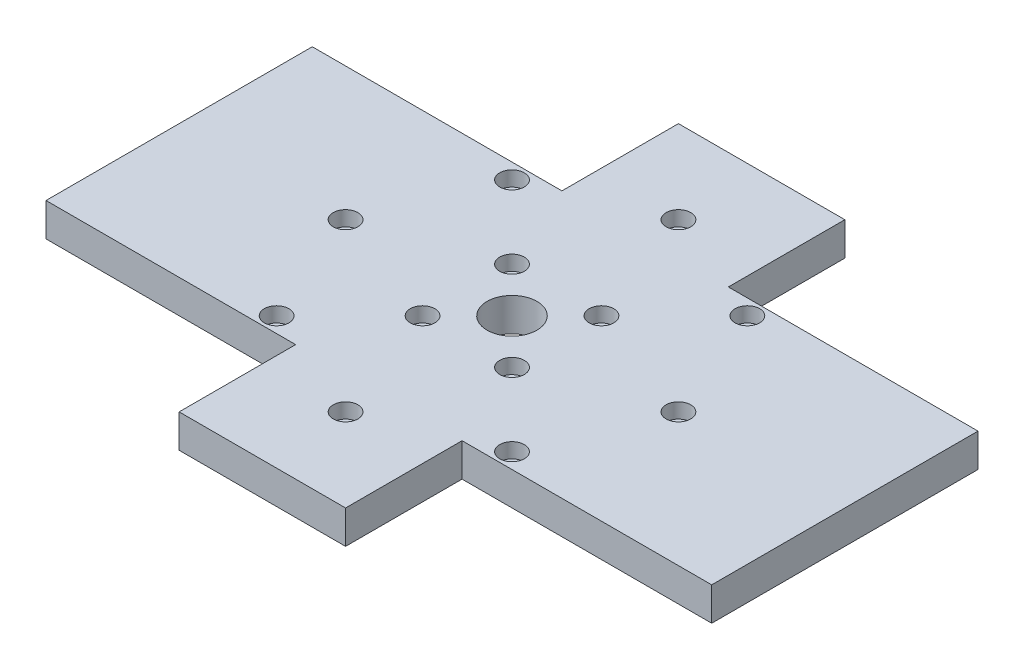
SolidWorks part; units mm, degrees
ref_plane "前视基准面" through (0, 0, 0) normal (0, 0, 1) x (1, 0, 0)
ref_plane "上视基准面" through (0, 0, 0) normal (0, 1, 0) x (1, 0, 0)
ref_plane "右视基准面" through (0, 0, 0) normal (1, 0, 0) x (0, 0, -1)
sketch "草图1" plane through (0, 0, 0) normal (0, 1, 0) x (1, 0, 0)
  line L1 (-100, 40) -> (100, 40)
  line L2 (-100, 40) -> (-100, -40)
  line L3 (-100, -40) -> (100, -40)
  line L4 (100, 40) -> (100, -40)
  line L5 (-100, 40) -> (100, -40) construction
  line L6 (-100, -40) -> (100, 40) construction
  point P0 (0, 0)
  dimension "D1" = 80
  dimension "D2" = 200
extrude "凸台-拉伸1" add sketch "草图1" along normal blind 10
sketch "草图3" plane through (0, 10, 0) normal (0, 1, 0) x (1, 0, 0)
  line L1 (-25, -75) -> (25, -75)
  line L2 (-25, -75) -> (-25, 75)
  line L3 (-25, 75) -> (25, 75)
  line L4 (25, -75) -> (25, 75)
  line L5 (-25, -75) -> (25, 75) construction
  line L6 (-25, 75) -> (25, -75) construction
  point P0 (0, 0)
  dimension "D1" = 150
  dimension "D2" = 50
extrude "凸台-拉伸2" add sketch "草图3" against normal blind 10
sketch "草图5" plane through (0, 10, 0) normal (0, 1, 0) x (1, 0, 0)
  line L0 (0, 0) -> (46.2802, 0) construction
  line L1 (0, 0) -> (16.9009, 16.9009) construction
  circle A0 centre (0, 0) radius 19 construction
  circle A1 centre (13.435, 13.435) radius 1.7
  circle A2 centre (13.435, -13.435) radius 1.7
  circle A3 centre (-13.435, -13.435) radius 1.7
  circle A4 centre (-13.435, 13.435) radius 1.7
  circle A5 centre (0, 0) radius 7.5
  point P16 (0, 0)
  dimension "D1" = 38
  dimension "D2" = 3.4
  dimension "D3" = 45
  dimension "D5" = 15
  dimension "D4" = 4
extrude "切除-拉伸3" cut sketch "草图5" against normal blind 10
sketch "草图6" plane through (0, 10, 0) normal (0, 1, 0) x (1, 0, 0)
  circle A0 centre (0, 0) radius 50 construction
  circle A1 centre (0, 50) radius 1.7
  circle A2 centre (35.3553, 35.3553) radius 1.7
  circle A3 centre (50, 0) radius 1.7
  circle A4 centre (35.3553, -35.3553) radius 1.7
  circle A5 centre (0, -50) radius 1.7
  circle A6 centre (-35.3553, -35.3553) radius 1.7
  circle A7 centre (-50, 0) radius 1.7
  circle A8 centre (-35.3553, 35.3553) radius 1.7
  point P22 (0, 0)
  dimension "D1" = 3.4
  dimension "D2" = 100
  dimension "D3" = 8
extrude "切除-拉伸4" cut sketch "草图6" against normal blind 10
sketch "草图7" plane through (0, 10, 0) normal (0, 1, 0) x (1, 0, 0)
  circle A0 centre (0, 50) radius 3.7
  circle A1 centre (13.435, 13.435) radius 3.7
  circle A2 centre (35.3553, 35.3553) radius 3.7
  circle A3 centre (50, 0) radius 3.7
  circle A4 centre (35.3553, -35.3553) radius 3.7
  circle A5 centre (0, -50) radius 3.7
  circle A6 centre (-35.3553, -35.3553) radius 3.7
  circle A7 centre (-50, 0) radius 3.7
  circle A8 centre (-35.3553, 35.3553) radius 3.7
  circle A9 centre (13.435, -13.435) radius 3.7
  circle A10 centre (-13.435, -13.435) radius 3.7
  circle A11 centre (-13.435, 13.435) radius 3.7
  point P23 (0, 0)
  point P30 (0, 0)
  dimension "D1" = 7.4
  dimension "D2" = 7.4
  dimension "D3" = 8
  dimension "D4" = 4
extrude "切除-拉伸5" cut sketch "草图7" against normal blind 4.5
